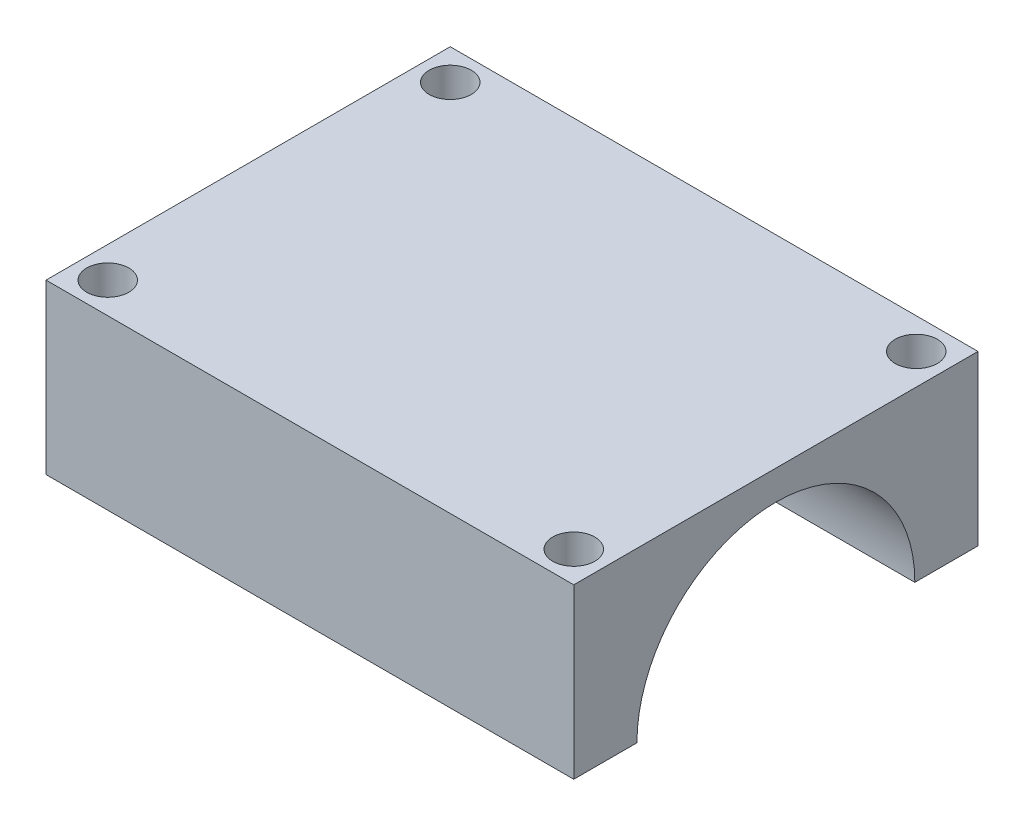
SolidWorks part; units mm, degrees
ref_plane "Front Plane" through (0, 0, 0) normal (0, 0, 1) x (1, 0, 0)
ref_plane "Top Plane" through (0, 0, 0) normal (0, 1, 0) x (1, 0, 0)
ref_plane "Right Plane" through (0, 0, 0) normal (1, 0, 0) x (0, 0, -1)
sketch "Sketch1" plane through (0, 0, 0) normal (0, 1, 0) x (1, 0, 0)
  line L1 (-23.5, -18) -> (23.5, -18)
  line L2 (-23.5, -18) -> (-23.5, 18)
  line L3 (-23.5, 18) -> (23.5, 18)
  line L4 (23.5, -18) -> (23.5, 18)
  line L5 (-23.5, -18) -> (23.5, 18) construction
  line L6 (-23.5, 18) -> (23.5, -18) construction
  point P0 (0, 0)
  dimension "D1" = 47
  dimension "D2" = 36
extrude "Boss-Extrude1" add sketch "Sketch1" along normal blind 30
sketch "Sketch3" plane through (23.5, 0, 0) normal (1, 0, 0) x (0, 0, -1)
  line L0 (0, 0) -> (0, 30) construction
  line L1 (-18, 0) -> (18, 0) construction
  line L2 (-18, 30) -> (18, 30) construction
  circle A0 centre (0, 15) radius 12.375
  dimension "D1" = 24.75
extrude "Cut-Extrude1" cut sketch "Sketch3" against normal blind 47
sketch "Sketch5" plane through (0, 30, 0) normal (0, 1, 0) x (1, 0, 0)
  line L7 (23.5, 18) -> (-23.5, 18) construction
  line L9 (-23.5, 18) -> (-23.5, -18) construction
  line L10 (0, 0) -> (0, 2.7791) construction
  line L11 (0, 2.7791) -> (0, 0) construction
  line L12 (0, 0) -> (-2.7536, 0) construction
  circle A1 centre (-20.75, 15.25) radius 1.875
  circle A2 centre (-20.75, -15.25) radius 1.875
  circle A3 centre (20.75, -15.25) radius 1.875
  circle A4 centre (20.75, 15.25) radius 1.875
  point P0 (0, 0)
  dimension "D2" = 3.75
  dimension "D3" = 2.75
  dimension "D4" = 2.75
extrude "Cut-Extrude2" cut sketch "Sketch5" against normal blind 40
sketch "Sketch7" plane through (0, 0, 0) normal (1, 0, 0) x (0, 0, -1)
  line L0 (-18, 30) -> (-18, 0) construction
  line L1 (-18, 15) -> (18, 15)
  line L2 (-18, 15) -> (-18, 0)
  line L3 (-18, 0) -> (18, 0)
  line L4 (18, 15) -> (18, 0)
extrude "Cut-Extrude3" cut sketch "Sketch7" against normal through all from surface at 23.5 starting at face at (23.5, 15, -12.375)
